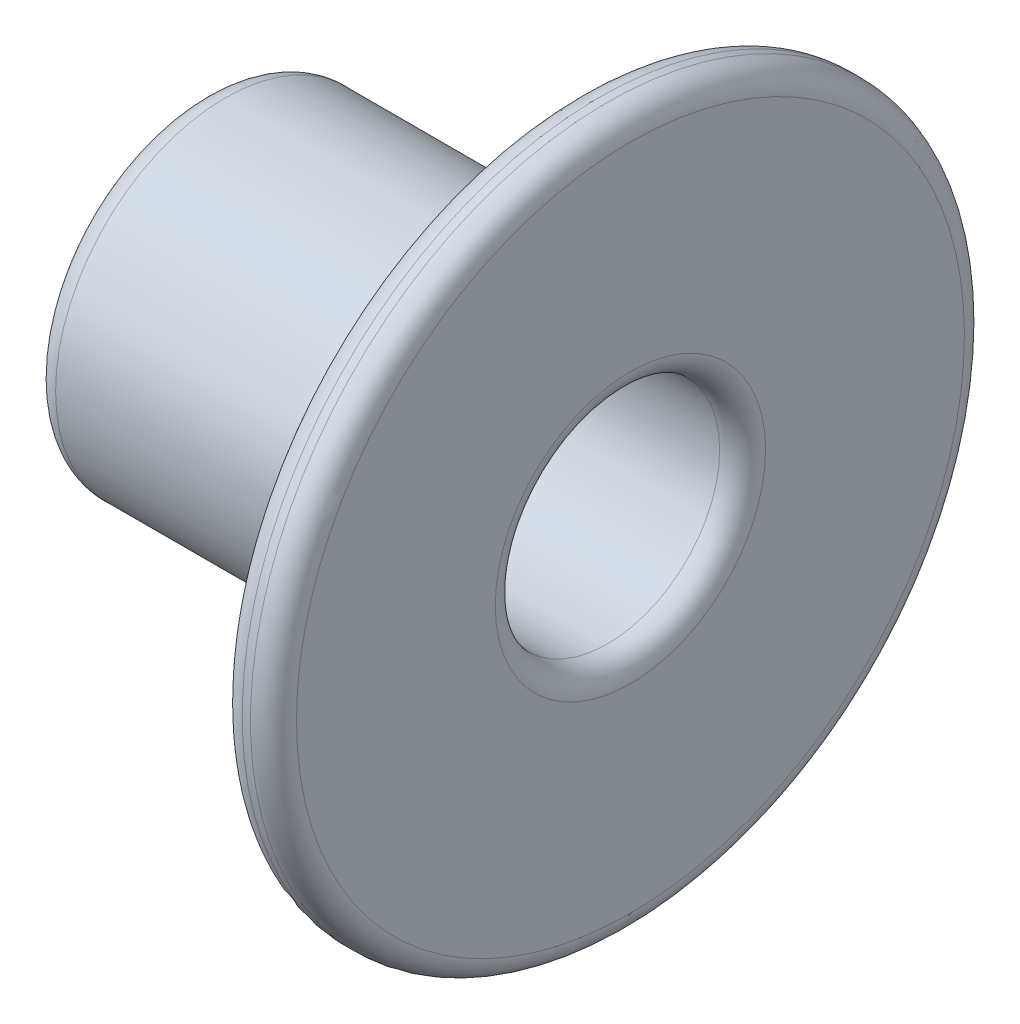
SolidWorks part; units mm, degrees
ref_plane "前视基准面" through (0, 0, 0) normal (0, 0, 1) x (1, 0, 0)
ref_plane "上视基准面" through (0, 0, 0) normal (0, 1, 0) x (1, 0, 0)
ref_plane "右视基准面" through (0, 0, 0) normal (1, 0, 0) x (0, 0, -1)
sketch "草图1" plane through (0, 0, 0) normal (0, 0, 1) x (1, 0, 0)
  line L0 (-455, 8.382) -> (-455, 0.277)
  line L1 (-455, 0.277) -> (-450, 0.277)
  line L2 (-450, 0.277) -> (-450, 6.477)
  line L3 (-450, 6.477) -> (-432.6124, 6.477)
  line L4 (-431.3424, 7.747) -> (-431.3424, 18.73)
  line L5 (-432.6124, 20) -> (-433.0724, 20)
  line L6 (-434.3424, 18.73) -> (-434.3424, 11.652)
  line L7 (-436.3424, 9.652) -> (-453.73, 9.652)
  line L8 (-455.0013, 0.277) -> (-431.3411, 0.277) construction
  line L9 (-450, 0.277) -> (-450, 9.652) construction
  arc A0 (-432.6124, 6.477) -> (-431.3424, 7.747) centre (-432.6124, 7.747) ccw
  arc A1 (-431.3424, 18.73) -> (-432.6124, 20) centre (-432.6124, 18.73) ccw
  arc A2 (-433.0724, 20) -> (-434.3424, 18.73) centre (-433.0724, 18.73) ccw
  arc A3 (-434.3424, 11.652) -> (-436.3424, 9.652) centre (-436.3424, 11.652) cw
  arc A4 (-453.73, 9.652) -> (-455, 8.382) centre (-453.73, 8.382) ccw
revolve "旋转1" add sketch "草图1" angle 360 about L8
